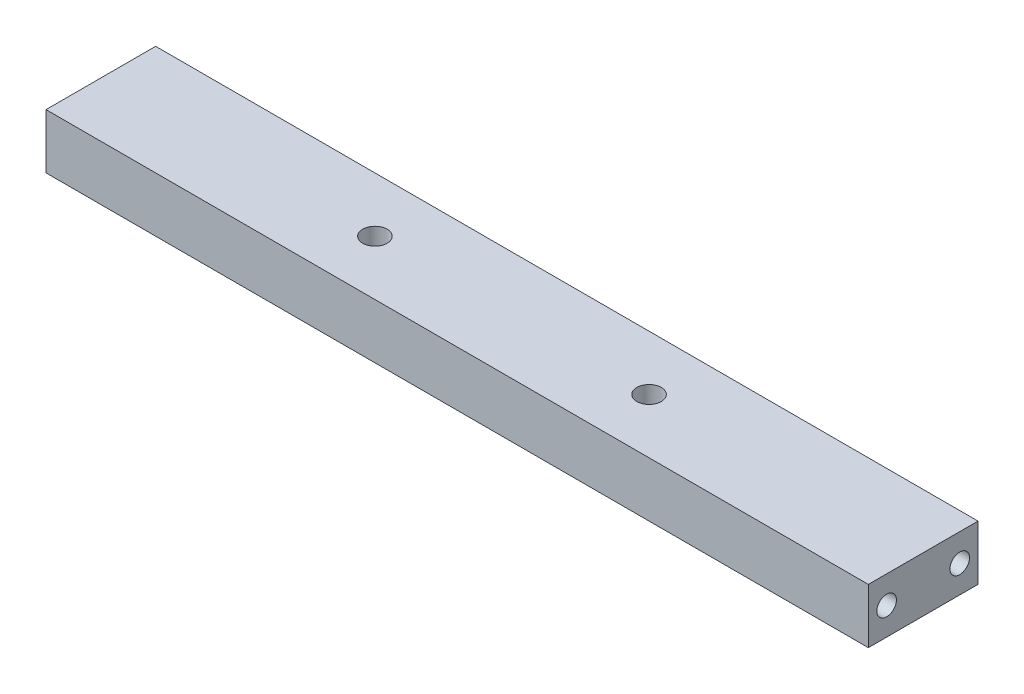
SolidWorks part; units mm, degrees
material "1060 Alloy"
ref_plane "Front Plane" through (0, 0, 0) normal (0, 0, 1) x (1, 0, 0)
ref_plane "Top Plane" through (0, 0, 0) normal (0, 1, 0) x (1, 0, 0)
ref_plane "Right Plane" through (0, 0, 0) normal (1, 0, 0) x (0, 0, -1)
sketch "ID_LENGTH" plane through (0, 0, 0) normal (0, 1, 0) x (1, 0, 0)
  line L0 (-146.05, 0) -> (146.05, 0) construction
  dimension "D1" = 292.1
sketch "CUT_LIST" plane through (0, 0, 0) normal (0, 1, 0) x (1, 0, 0)
  line L0 (-138.1125, 0) -> (138.1125, 0) construction
  dimension "D1" = 276.225
sketch "Sketch1" plane through (0, 0, 0) normal (1, 0, 0) x (0, 0, -1)
  line L0 (-19.05, -9.525) -> (19.05, 9.525) construction
  line L1 (-19.05, 9.525) -> (19.05, 9.525)
  line L2 (-19.05, 9.525) -> (-19.05, -9.525)
  line L3 (-19.05, -9.525) -> (19.05, -9.525)
  line L4 (19.05, 9.525) -> (19.05, -9.525)
  dimension "D1" = 19.05
  dimension "D2" = 38.1
extrude "Extrude1" add sketch "Sketch1" along normal mid plane 285.75
hole_wizard "M8x1.25 Tapped Hole1" positions "Sketch3" profile "Sketch2" tap size "M8x1.25" standard "Ansi Metric"
sketch "Sketch3" plane through (142.875, 0, 0) normal (1, 0, 0) x (0, 0, -1)
  line L0 (-12.7, 0) -> (12.7, 0) construction
  point P0 (-12.7, 0)
  point P1 (12.7, 0)
  dimension "D1" = 25.4
cosmetic thread "Hole Thread1" parameters "D1"=16.002, "D2"=8
cosmetic thread "Hole Thread2" parameters "D1"=16.002, "D2"=8
sketch "Sketch2" plane through (142.875, 0, 12.7) normal (0, 1, 0) x (0, 0, -1)
  line L0 (0, 0) -> (0, 21.8041)
  line L1 (0, 21.8041) -> (3.4, 19.7612)
  line L2 (3.4, 19.7612) -> (3.4, 0)
  line L5 (3.4, 0) -> (0, 0)
  line L10 (0, 21.8041) -> (-3.4, 19.7612) construction
  line L11 (0, -6.35) -> (0, 107.95) construction
  dimension "Tap Drill Dia." = 6.8
  dimension "Tap Drill Depth" = 19.7612
  dimension "Drill Angle" = 118
mirror "Mirror1" about plane through (0, 0, 0) normal (1, 0, 0) of "M8x1.25 Tapped Hole1"
hole_wizard "M10x1.5 Tapped Hole1" positions "Sketch14" profile "Sketch13" tap size "M10x1.5" standard "ANSI Metric" end condition through all
sketch "Sketch14" plane through (0, 9.525, 0) normal (0, 1, 0) x (-1, 0, 0)
  line L0 (-47.625, 0) -> (47.625, 0) construction
  point P0 (47.625, 0)
  point P5 (-47.625, 0)
  point P18 (0, 0)
  dimension "D2" = 95.25
cosmetic thread "Hole Thread13" parameters "D2"=10
cosmetic thread "Hole Thread16" parameters "D2"=10
sketch "Sketch13" plane through (-47.625, 9.525, 0) normal (1, 0, 0) x (0, 0, 1)
  line L0 (0, 0) -> (0, 19.05)
  line L1 (0, 19.05) -> (4.25, 19.05)
  line L2 (4.25, 19.05) -> (4.25, 0)
  line L5 (4.25, 0) -> (0, 0)
  line L11 (0, -6.35) -> (0, 107.95) construction
  dimension "Thru Tap Drill Dia." = 8.5
  dimension "Thru Tap Drill Depth" = 19.05
hole_wizard "M5x0.8 Tapped Hole2" positions "Sketch16" profile "Sketch17" tap size "M5x0.8" standard "ANSI Metric"
sketch "Sketch16" plane through (-9.0513, 7.1737, -19.05) normal (0, 0, 1) x (1, 0, 0)
  line L0 (-54.4487, -7.1737) -> (72.5513, -7.1737) construction
  point P0 (72.5513, -7.1737)
  point P1 (-54.4487, -7.1737)
  point P7 (9.0513, -7.1737)
  dimension "D1" = 127
sketch "Sketch17" plane through (63.5, 0, -19.05) normal (1, 0, 0) x (0, 1, 0)
  line L0 (0, 0) -> (0, 13.657)
  line L1 (0, 13.657) -> (2.1, 12.3952)
  line L2 (2.1, 12.3952) -> (2.1, 0)
  line L5 (2.1, 0) -> (0, 0)
  line L10 (0, 13.657) -> (-2.1, 12.3952) construction
  line L11 (0, -6.35) -> (0, 107.95) construction
  dimension "Tap Drill Dia." = 4.2
  dimension "Tap Drill Depth" = 12.3952
  dimension "Drill Angle" = 118
cosmetic thread "Hole Thread23" parameters "D1"=10.0076, "D2"=5
cosmetic thread "Hole Thread24" parameters "D1"=10.0076, "D2"=5
hole_wizard "M5x0.8 Tapped Hole3" positions "Sketch23" profile "Sketch22" tap size "M5x0.8" standard "ANSI Metric"
sketch "Sketch23" plane through (0, -9.525, 0) normal (0, -1, 0) x (-1, 0, 0)
  line L0 (19.05, 12.7) -> (-19.05, 12.7) construction
  line L1 (-19.05, 12.7) -> (-19.05, -12.7) construction
  point P0 (-19.05, 12.7)
  point P2 (19.05, 12.7)
  point P4 (19.05, -12.7)
  point P6 (-19.05, -12.7)
  point P14 (0, 12.7)
  point P16 (-19.05, 0)
  dimension "D1" = 38.1
  dimension "D2" = 25.4
sketch "Sketch22" plane through (19.05, -9.525, -12.7) normal (1, 0, 0) x (0, 0, -1)
  line L0 (0, 0) -> (0, 13.657)
  line L1 (0, 13.657) -> (2.1, 12.3952)
  line L2 (2.1, 12.3952) -> (2.1, 0)
  line L5 (2.1, 0) -> (0, 0)
  line L10 (0, 13.657) -> (-2.1, 12.3952) construction
  line L11 (0, -6.35) -> (0, 107.95) construction
  dimension "Tap Drill Dia." = 4.2
  dimension "Tap Drill Depth" = 12.3952
  dimension "Drill Angle" = 118
cosmetic thread "Hole Thread25" parameters "D1"=10.0076, "D2"=5
cosmetic thread "Hole Thread26" parameters "D1"=10.0076, "D2"=5
cosmetic thread "Hole Thread27" parameters "D1"=10.0076, "D2"=5
cosmetic thread "Hole Thread28" parameters "D1"=10.0076, "D2"=5
equation "\"D1@CUT_LIST\" = \"MountLength@Extrude1\" + .125"
